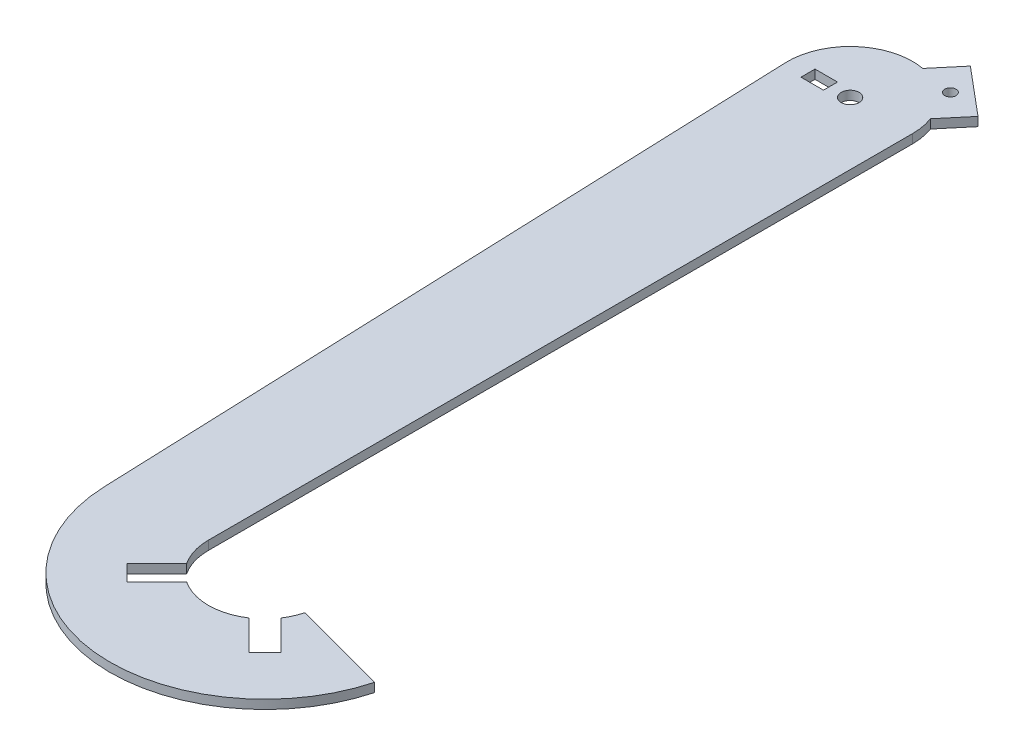
SolidWorks part; units mm, degrees
ref_plane "Front Plane" through (0, 0, 0) normal (0, 0, 1) x (1, 0, 0)
ref_plane "Top Plane" through (0, 0, 0) normal (0, 1, 0) x (1, 0, 0)
ref_plane "Right Plane" through (0, 0, 0) normal (1, 0, 0) x (0, 0, -1)
sketch "Sketch1" plane through (0, 0, 0) normal (0, 1, 0) x (1, 0, 0)
  line L0 (22.225, 0) -> (22.225, -250.4484)
  line L1 (-22.2093, -0.8359) -> (-12.736, -252.521)
  line L2 (20.84, 7.7231) -> (28.5534, 16.9157)
  line L3 (28.5534, 16.9157) -> (11.7004, 31.057)
  line L4 (11.7004, 31.057) -> (3.987, 21.8645)
  line L5 (0, 0) -> (20.1269, 23.9863) construction
  line L6 (25.5686, -261.55) -> (14.962, -272.1566)
  line L7 (14.962, -272.1566) -> (20.6188, -277.8135)
  line L8 (20.6188, -277.8135) -> (31.2254, -267.2069)
  line L9 (53.4286, -267.2069) -> (64.0352, -277.8135)
  line L10 (64.0352, -277.8135) -> (69.692, -272.1566)
  line L11 (69.692, -272.1566) -> (59.0854, -261.55)
  line L12 (61.744, -255.6512) -> (95.5514, -264.7099)
  line L13 (116.8683, -175.9072) -> (109.8554, -182.92) construction
  line L14 (-81.3975, -126.724) -> (35273.9416, -35482.063) construction
  line L15 (42.327, -343.0909) -> (42.327, 49656.9091) construction
  line L16 (0, 0) -> (42.327, -250.4484) construction
  line L17 (7.8437, 26.4607) -> (24.6967, 12.3194) construction
  line L18 (-15, 2.5) -> (-7, 2.5)
  line L19 (-15, 2.5) -> (-15, -2.5)
  line L20 (-15, -2.5) -> (-7, -2.5)
  line L21 (-7, 2.5) -> (-7, -2.5)
  arc A0 (20.84, 7.7231) -> (22.225, 0) centre (0, 0) cw
  arc A1 (-22.2093, -0.8359) -> (3.987, 21.8645) centre (0, 0) cw
  arc A2 (22.225, -250.4484) -> (25.5686, -261.55) centre (42.327, -250.4484) ccw
  arc A3 (-12.736, -252.521) -> (95.5514, -264.7099) centre (42.327, -250.4484) ccw
  arc A4 (31.2254, -267.2069) -> (53.4286, -267.2069) centre (42.327, -250.4484) ccw
  arc A5 (59.0854, -261.55) -> (61.744, -255.6512) centre (42.327, -250.4484) ccw
  circle A6 centre (0, 0) radius 3.175
  circle A7 centre (16.2702, 19.3901) radius 2
  circle A8 centre (42.327, -250.4484) radius 12.7 construction
  point P31 (42.327, -270.5504)
  point P32 (66.8636, -274.9851)
  point P33 (24.6967, 12.3194)
  point P36 (7.8437, 26.4607)
  point P37 (-7, 0)
  point P43 (20.1269, 23.9863)
  dimension "D1" = 22.225
  dimension "D2" = 6.35
  dimension "D7" = 25.4
  dimension "D12" = 4
  dimension "D3" = 45
  dimension "D4" = 45
  dimension "D5" = 8
  dimension "D6" = 15
  dimension "D8" = 34.7
  dimension "D9" = 35
  dimension "D10" = 254
  dimension "D11" = 60
  dimension "D13" = 12
  dimension "D14" = 22
  dimension "D15" = 50
  dimension "D16" = 8
  dimension "D17" = 5
  dimension "D18" = 7
extrude "Boss-Extrude1" add sketch "Sketch1" along normal mid plane 3.175
